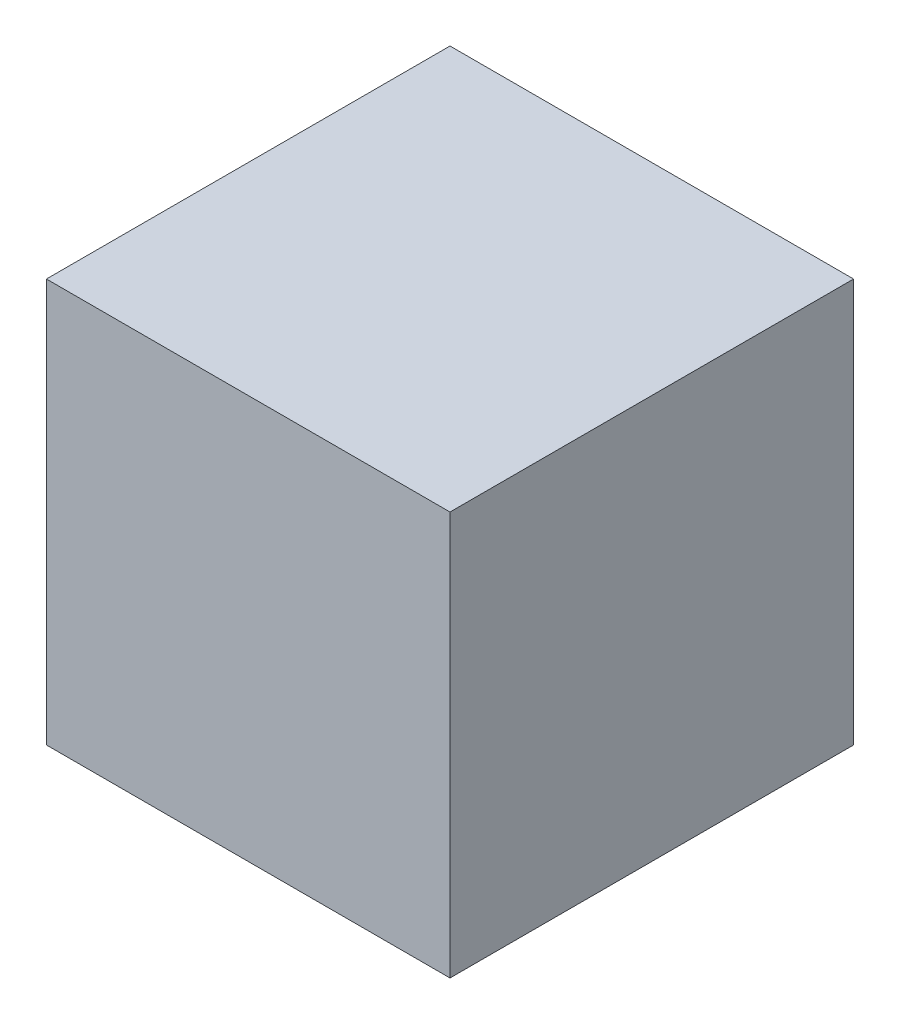
SolidWorks part; units mm, degrees
ref_plane "Front Plane" through (0, 0, 0) normal (0, 0, 1) x (1, 0, 0)
ref_plane "Top Plane" through (0, 0, 0) normal (0, 1, 0) x (1, 0, 0)
ref_plane "Right Plane" through (0, 0, 0) normal (1, 0, 0) x (0, 0, -1)
sketch "Sketch1" plane through (0, 0, 0) normal (0, 0, 1) x (1, 0, 0)
  line L1 (-50, 50) -> (50, 50)
  line L2 (-50, 50) -> (-50, -50)
  line L3 (-50, -50) -> (50, -50)
  line L4 (50, 50) -> (50, -50)
  line L5 (0, -50) -> (0, 50) construction
  line L6 (-50, 0) -> (50, 0) construction
  point P0 (0, 0)
  dimension "D1" = 100
  dimension "D2" = 100
extrude "Boss-Extrude1" add sketch "Sketch1" along normal blind 100
